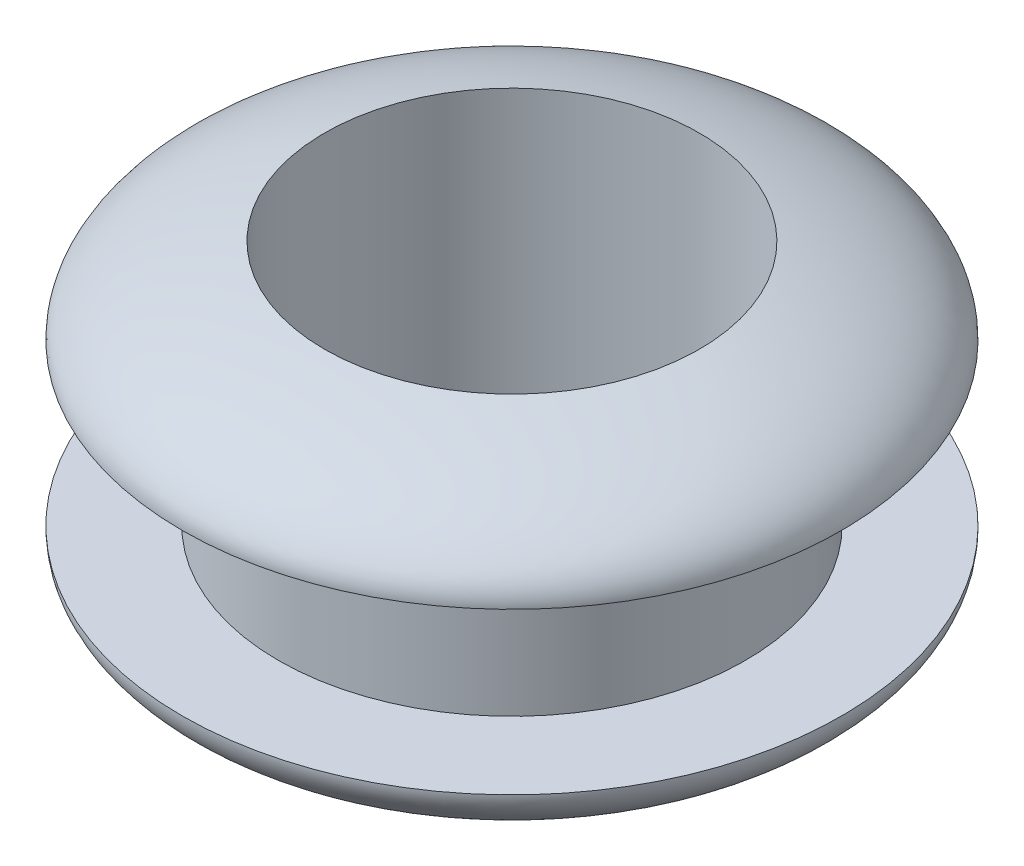
SolidWorks part; units mm, degrees
ref_plane "前视基准面" through (0, 0, 0) normal (0, 0, 1) x (1, 0, 0)
ref_plane "上视基准面" through (0, 0, 0) normal (0, 1, 0) x (1, 0, 0)
ref_plane "右视基准面" through (0, 0, 0) normal (1, 0, 0) x (0, 0, -1)
sketch "草图1" plane through (0, 0, 0) normal (1, 0, 0) x (0, 0, -1)
  line L0 (-6.4534, 0) -> (8.2428, 0) construction
  line L1 (0, 6.5163) -> (0, -8.9731) construction
  line L2 (4.36, -1.5) -> (6.1555, -1.5)
  line L3 (4.36, 1.5) -> (4.36, -1.5)
  line L4 (4.36, 1.5) -> (6.1555, 1.5)
  line L5 (0, 3.5) -> (0, -3.5)
  ellipse E0 centre (0, 1.623) end of major axis (6.1555, 1.5) minor radius 1.8766 (6.1555, 1.5) -> (0, 3.5) ccw
  ellipse E1 centre (0, -1.623) end of major axis (6.1555, -1.5) minor radius 1.8766 (6.1555, -1.5) -> (0, -3.5) cw
  point P22 (4.36, 0)
  dimension "D1" = 4.36
  dimension "D2" = 1.5
  dimension "D3" = 3.5
revolve "旋转1" add sketch "草图1" angle 360 about L1
ref_plane "基准面1" through (0, 4.5, 0) normal (0, 1, 0) x (1, 0, 0)
sketch "草图2" plane through (0, 4.5, 0) normal (0, 1, 0) x (1, 0, 0)
  circle A0 centre (0, 0) radius 3.5
  dimension "D1" = 7
extrude "切除-拉伸1" cut sketch "草图2" against normal through all
